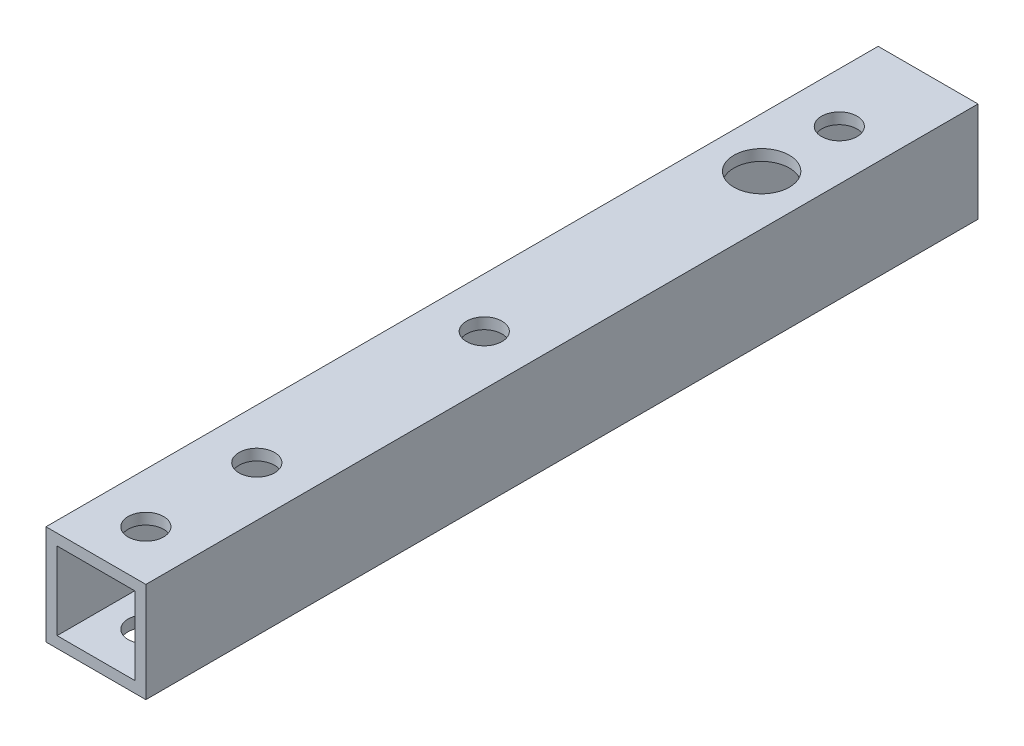
SolidWorks part; units mm, degrees
ref_plane "正面" through (0, 0, 0) normal (0, 0, 1) x (1, 0, 0)
ref_plane "平面" through (0, 0, 0) normal (0, 1, 0) x (1, 0, 0)
ref_plane "右側面" through (0, 0, 0) normal (1, 0, 0) x (0, 0, -1)
sketch "ｽｹｯﾁ1" plane through (0, 0, 0) normal (0, 0, 1) x (1, 0, 0)
  line L1 (-4.5, 4.5) -> (4.5, 4.5)
  line L2 (-4.5, 4.5) -> (-4.5, -4.5)
  line L3 (-4.5, -4.5) -> (4.5, -4.5)
  line L4 (4.5, 4.5) -> (4.5, -4.5)
  line L5 (-4.5, 4.5) -> (4.5, -4.5) construction
  line L6 (-4.5, -4.5) -> (4.5, 4.5) construction
  line L7 (-3.5, 3.5) -> (3.5, 3.5)
  line L8 (-3.5, 3.5) -> (-3.5, -3.5)
  line L9 (-3.5, -3.5) -> (3.5, -3.5)
  line L10 (3.5, 3.5) -> (3.5, -3.5)
  line L11 (-3.5, 3.5) -> (3.5, -3.5) construction
  line L12 (-3.5, -3.5) -> (3.5, 3.5) construction
  point P0 (0, 0)
  point P6 (0, 0)
  dimension "D1" = 7
  dimension "D2" = 7
  dimension "D3" = 9
  dimension "D4" = 9
extrude "ﾎﾞｽ - 押し出し1" add sketch "ｽｹｯﾁ1" along normal blind 70
sketch "ｽｹｯﾁ2" plane through (0, 4.5, 0) normal (0, 1, 0) x (1, 0, 0)
  line L0 (0, 0) -> (0, -10)
  line L1 (0, -10) -> (0, -17)
  circle A0 centre (0, -10) radius 2.5
  circle A1 centre (0, -17) radius 1.6
  dimension "D3" = 3.2
  dimension "D4" = 5
  dimension "D1" = 10
  dimension "D2" = 7
extrude "ｶｯﾄ - 押し出し1" cut sketch "ｽｹｯﾁ2" against normal blind 100 contours L1 A0 L0 | L0 A0 L1
sketch "ｽｹｯﾁ3" plane through (0, 4.5, 0) normal (0, 1, 0) x (1, 0, 0)
  line L0 (0, -10) -> (0, -3)
  circle A0 centre (0, -3) radius 1.6
  dimension "D2" = 3.2
  dimension "D1" = 7
extrude "ｶｯﾄ - 押し出し2" cut sketch "ｽｹｯﾁ3" against normal blind 100
sketch "ｽｹｯﾁ4" plane through (0, 4.5, 0) normal (0, 1, 0) x (1, 0, 0)
  line L0 (0, -70) -> (0, -65.5)
  line L1 (4.5, -70) -> (-4.5, -70) construction
  line L2 (0, -65.5) -> (0, -55.5)
  circle A0 centre (0, -65.5) radius 1.6
  circle A1 centre (0, -55.5) radius 1.6
  dimension "D2" = 3.2
  dimension "D4" = 3.2
  dimension "D1" = 4.5
  dimension "D3" = 10
extrude "ｶｯﾄ - 押し出し3" cut sketch "ｽｹｯﾁ4" against normal blind 100
sketch "ｽｹｯﾁ5" plane through (0, 4.5, 0) normal (0, 1, 0) x (1, 0, 0)
  line L0 (0, 0) -> (0, -35)
  circle A0 centre (0, -35) radius 1.6
  dimension "D2" = 3.2
  dimension "D1" = 35
extrude "ｶｯﾄ - 押し出し4" cut sketch "ｽｹｯﾁ5" against normal through all
sketch "ｽｹｯﾁ6" plane through (0, 0, 0) normal (0, 0, -1) x (-1, 0, 0)
  line L1 (4.5, -4.5) -> (-4.5, -4.5)
  line L2 (4.5, -4.5) -> (4.5, 4.5)
  line L3 (4.5, 4.5) -> (-4.5, 4.5)
  line L4 (-4.5, -4.5) -> (-4.5, 4.5)
  line L5 (4.5, -4.5) -> (-4.5, 4.5) construction
  line L6 (4.5, 4.5) -> (-4.5, -4.5) construction
  line L7 (3.5, -3.5) -> (-3.5, -3.5)
  line L8 (3.5, -3.5) -> (3.5, 3.5)
  line L9 (3.5, 3.5) -> (-3.5, 3.5)
  line L10 (-3.5, -3.5) -> (-3.5, 3.5)
  line L11 (3.5, -3.5) -> (-3.5, 3.5) construction
  line L12 (3.5, 3.5) -> (-3.5, -3.5) construction
  point P0 (0, 0)
  point P7 (0, 0)
extrude "ﾎﾞｽ - 押し出し2" add sketch "ｽｹｯﾁ6" along normal blind 5
